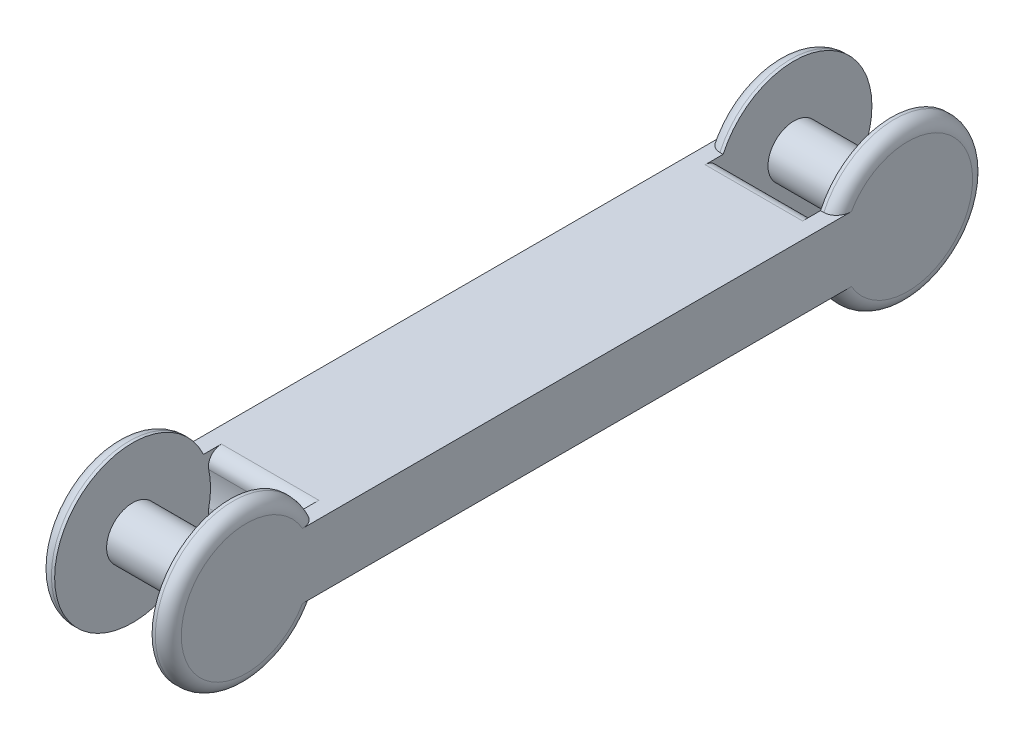
SolidWorks part; units mm, degrees
ref_plane "Front Plane" through (0, 0, 0) normal (0, 0, 1) x (1, 0, 0)
ref_plane "Top Plane" through (0, 0, 0) normal (0, 1, 0) x (1, 0, 0)
ref_plane "Right Plane" through (0, 0, 0) normal (1, 0, 0) x (0, 0, -1)
sketch "Sketch1" plane through (0, 0, 0) normal (1, 0, 0) x (0, 0, -1)
  line L0 (0, 0) -> (-40, 0)
  line L1 (-40, -10) -> (0, -10)
  line L2 (0, -10) -> (0, 0)
  arc A0 (-40, 0) -> (-40, -10) centre (-50.9087, -5) ccw
  dimension "D1" = 12
  dimension "D2" = 5
  dimension "D3" = 10
  dimension "D4" = 40
extrude "Boss-Extrude1" add sketch "Sketch1" along normal blind 20
sketch "Sketch2" plane through (20, 0, 0) normal (1, 0, 0) x (0, 0, -1)
  circle A0 centre (-50.9087, -5) radius 4
  circle A1 centre (-50.9087, -5) radius 12
  dimension "D1" = 8
extrude "Cut-Extrude1" cut sketch "Sketch2" against normal blind 15 from offset 2.5 offset against normal yes
fillet "Fillet1" radius 2 4 edges at (0, -5, 62.9087) (20, -5, 62.9087) (10, -10, 40) (10, 0, 40)
mirror "Mirror1" about plane through (20, -10, 0) normal (0, 0, 1) of "Cut-Extrude1", "Fillet1", "Boss-Extrude1"
